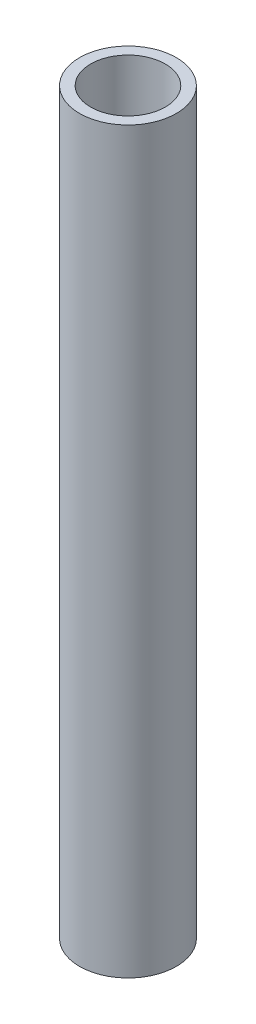
SolidWorks part; units mm, degrees
ref_plane "Front Plane" through (0, 0, 0) normal (0, 0, 1) x (1, 0, 0)
ref_plane "Top Plane" through (0, 0, 0) normal (0, 1, 0) x (1, 0, 0)
ref_plane "Right Plane" through (0, 0, 0) normal (1, 0, 0) x (0, 0, -1)
sketch "Sketch1" plane through (0, 0, 0) normal (0, 1, 0) x (1, 0, 0)
  circle A0 centre (0, 0) radius 2.85
extrude "Boss-Extrude1" add sketch "Sketch1" along normal blind 43.5
sketch "Sketch2" plane through (0, 43.5, 0) normal (0, 1, 0) x (1, 0, 0)
  circle A0 centre (0, 0) radius 2.2
extrude "Cut-Extrude1" cut sketch "Sketch2" against normal blind 40
